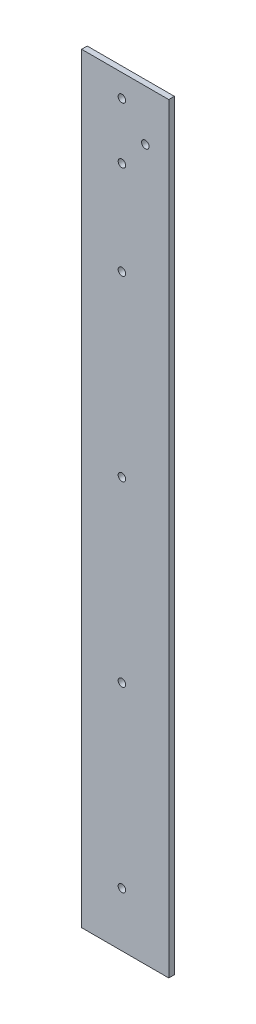
SolidWorks part; units mm, degrees
ref_plane "Front Plane" through (0, 0, 0) normal (0, 0, 1) x (1, 0, 0)
ref_plane "Top Plane" through (0, 0, 0) normal (0, 1, 0) x (1, 0, 0)
ref_plane "Right Plane" through (0, 0, 0) normal (1, 0, 0) x (0, 0, -1)
sketch "Sketch1" plane through (0, 0, 0) normal (0, 0, 1) x (1, 0, 0)
  line L0 (-22.6921, 203.279) -> (23.8079, 203.279)
  line L1 (-22.6921, 203.279) -> (-22.6921, -202.721)
  line L2 (-22.6921, -202.721) -> (23.8079, -202.721)
  line L3 (23.8079, 203.279) -> (23.8079, -202.721)
  circle A0 centre (-1.1921, 191.279) radius 2 construction
  circle A1 centre (-1.1921, 191.279) radius 2
  circle A2 centre (11.3079, 176.279) radius 2 construction
  circle A3 centre (11.3079, 176.279) radius 2
  circle A4 centre (-1.1921, 161.279) radius 2 construction
  circle A5 centre (-1.1921, 161.279) radius 2
  circle A6 centre (-1.1921, 111.279) radius 2 construction
  circle A7 centre (-1.1921, 111.279) radius 2
  circle A8 centre (-1.1921, 16.279) radius 2 construction
  circle A9 centre (-1.1921, 16.279) radius 2
  circle A10 centre (-1.1921, -78.721) radius 2 construction
  circle A11 centre (-1.1921, -78.721) radius 2
  circle A12 centre (-1.1921, -173.721) radius 2 construction
  circle A13 centre (-1.1921, -173.721) radius 2
  dimension "D1" = 46.5
  dimension "D2" = 406
extrude "Boss-Extrude1" add sketch "Sketch1" along normal blind 3
